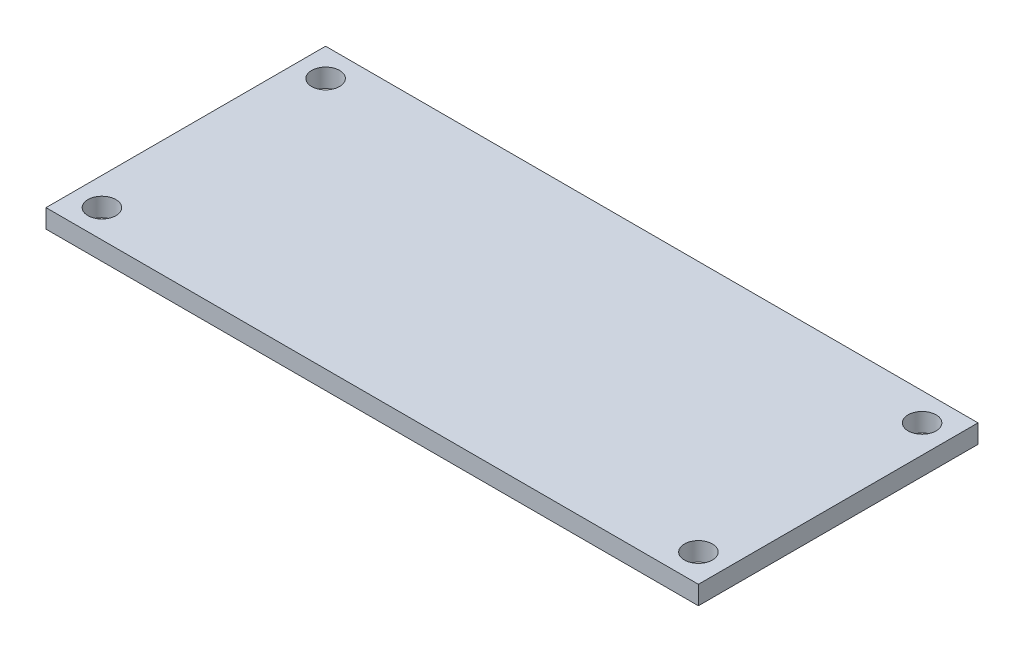
SolidWorks part; units mm, degrees
ref_plane "Front Plane" through (0, 0, 0) normal (0, 0, 1) x (1, 0, 0)
ref_plane "Top Plane" through (0, 0, 0) normal (0, 1, 0) x (1, 0, 0)
ref_plane "Right Plane" through (0, 0, 0) normal (1, 0, 0) x (0, 0, -1)
sketch "Sketch1" plane through (0, 0, 0) normal (0, 1, 0) x (1, 0, 0)
  line L1 (35, 15) -> (-35, 15)
  line L2 (35, 15) -> (35, -15)
  line L3 (35, -15) -> (-35, -15)
  line L4 (-35, 15) -> (-35, -15)
  line L5 (35, 15) -> (-35, -15) construction
  line L6 (35, -15) -> (-35, 15) construction
  point P0 (0, 0)
  dimension "D1" = 70
  dimension "D2" = 30
extrude "Boss-Extrude1" add sketch "Sketch1" along normal blind 2
sketch "Sketch2" plane through (0, 2, 0) normal (0, 1, 0) x (1, 0, 0)
  line L0 (0, 15) -> (0, -15) construction
  line L1 (35, 15) -> (-35, 15) construction
  line L2 (-35, -15) -> (35, -15) construction
  line L3 (-35, 15) -> (-35, -15) construction
  circle A0 centre (-32, 12) radius 1.5
  circle A1 centre (-32, -12) radius 1.5
  circle A2 centre (32, -12) radius 1.5
  circle A3 centre (32, 12) radius 1.5
  dimension "D1" = 3
  dimension "D2" = 3
  dimension "D3" = 3
  dimension "D4" = 3
  dimension "D5" = 3
  dimension "D6" = 3
extrude "Cut-Extrude1" cut sketch "Sketch2" against normal blind 2
